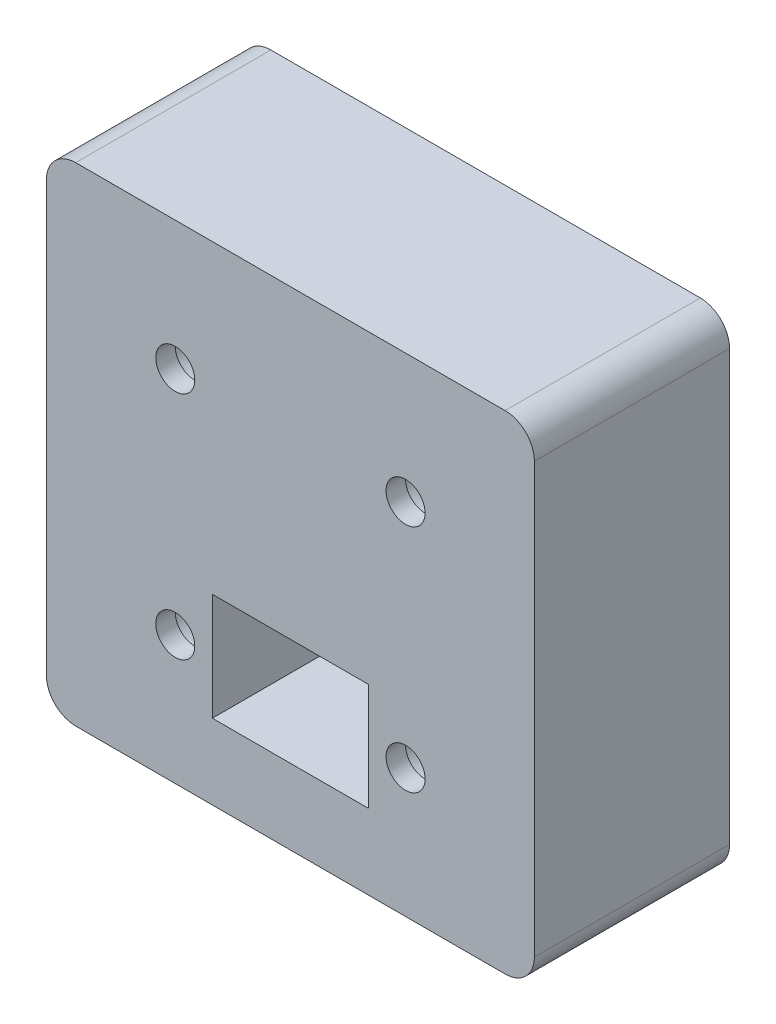
SolidWorks part; units mm, degrees
ref_plane "Front Plane" through (0, 0, 0) normal (0, 0, 1) x (1, 0, 0)
ref_plane "Top Plane" through (0, 0, 0) normal (0, 1, 0) x (1, 0, 0)
ref_plane "Right Plane" through (0, 0, 0) normal (1, 0, 0) x (0, 0, -1)
sketch "Sketch1" plane through (0, 0, 0) normal (0, 0, 1) x (1, 0, 0)
  line L1 (-25, -25) -> (25, -25)
  line L2 (-25, -25) -> (-25, 25)
  line L3 (-25, 25) -> (25, 25)
  line L4 (25, -25) -> (25, 25)
  line L5 (-25, -25) -> (25, 25) construction
  line L6 (-25, 25) -> (25, -25) construction
  line L7 (55, 0) -> (-55, 0) construction
  line L8 (0, -55) -> (0, 55) construction
  line L9 (11.8, -11.8) -> (-11.8, -11.8) construction
  line L11 (-8, -17.3) -> (8, -17.3)
  line L12 (-8, -17.3) -> (-8, -6.3)
  line L13 (-8, -6.3) -> (8, -6.3)
  line L14 (8, -17.3) -> (8, -6.3)
  line L15 (-8, -17.3) -> (8, -6.3) construction
  line L16 (-8, -6.3) -> (8, -17.3) construction
  circle A0 centre (-11.8, 11.8) radius 2
  circle A1 centre (-11.8, -11.8) radius 2
  circle A2 centre (11.8, -11.8) radius 2
  circle A3 centre (11.8, 11.8) radius 2
  point P0 (0, 0)
  point P5 (0, 0)
  point P21 (0, -11.8)
  point P22 (0, -11.8)
  dimension "D2" = 4
  dimension "D1" = 50
  dimension "D3" = 23.6
  dimension "D4" = 16
  dimension "D5" = 11
extrude "Boss-Extrude1" add sketch "Sketch1" along normal blind 2
sketch "Sketch2" plane through (0, 0, 0) normal (0, 0, -1) x (-1, 0, 0)
  line L0 (0, 1.1) -> (0, -1.1) construction
  line L1 (1.1, 0) -> (-1.1, 0) construction
  line L3 (25, -25) -> (-25, -25)
  line L4 (25, -25) -> (25, 25)
  line L5 (25, 25) -> (-25, 25)
  line L6 (-25, -25) -> (-25, 25)
  line L7 (25, -25) -> (-25, 25) construction
  line L8 (25, 25) -> (-25, -25) construction
  line L9 (8, -17.3) -> (-8, -17.3)
  line L10 (8, -17.3) -> (8, -6.3)
  line L11 (8, -6.3) -> (-8, -6.3)
  line L12 (-8, -17.3) -> (-8, -6.3)
  line L13 (8, -17.3) -> (-8, -6.3) construction
  line L14 (8, -6.3) -> (-8, -17.3) construction
  circle A0 centre (-11.8, -11.8) radius 3.1
  circle A1 centre (-11.8, -11.8) radius 2 construction
  circle A2 centre (11.8, -11.8) radius 3.1
  circle A3 centre (11.8, 11.8) radius 3.1
  circle A4 centre (-11.8, 11.8) radius 3.1
  point P2 (0, 0)
  point P15 (0, 0)
  point P21 (0, 0)
  point P23 (0, -11.8)
  point P29 (0, 0)
  dimension "D1" = 6.2
extrude "Boss-Extrude2" add sketch "Sketch2" along normal blind 18
fillet "Fillet1" radius 3 4 edges at (-25, 25, -8) (25, 25, -8) (25, -25, -8) (-25, -25, -8)
